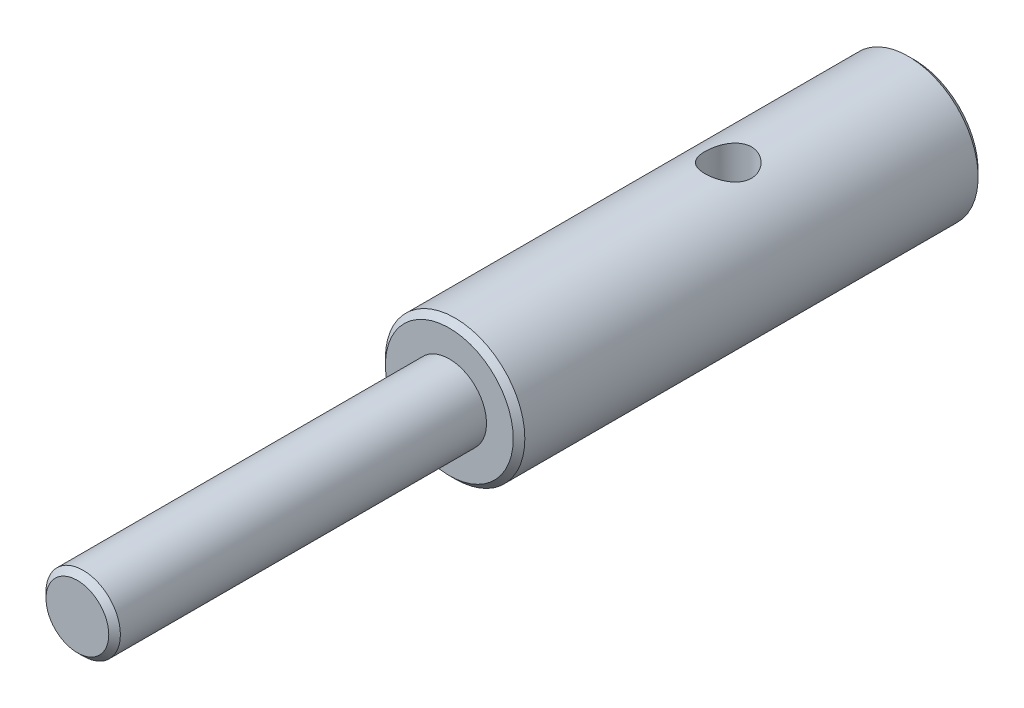
SolidWorks part; units mm, degrees
material "Unlegierter Baustahl"
ref_plane "Ebene vorne" through (0, 0, 0) normal (0, 0, 1) x (1, 0, 0)
ref_plane "Ebene oben" through (0, 0, 0) normal (0, 1, 0) x (1, 0, 0)
ref_plane "Ebene rechts" through (0, 0, 0) normal (1, 0, 0) x (0, 0, -1)
sketch "Skizze1" plane through (0, 0, 0) normal (1, 0, 0) x (0, 0, -1)
  line L0 (0, 0) -> (-32.0536, 0) construction
  line L1 (0, 1) -> (10, 1)
  line L2 (10, 1) -> (10, 3)
  line L3 (10, 3) -> (-10, 3)
  line L4 (0, 1) -> (0, 0)
  line L5 (0, 0) -> (-26, 0)
  line L6 (-26, 0) -> (-26, 1.6)
  line L7 (0, 3) -> (0, 0) construction
  line L8 (-26, 1.6) -> (-10, 1.6)
  line L9 (-10, 1.6) -> (-10, 3)
  dimension "D1" = 2
  dimension "D2" = 10
  dimension "D3" = 6
  dimension "D4" = 20
  dimension "D5" = 16
  dimension "D6" = 3.2
revolve "Rotation1" add sketch "Skizze1" angle 360 about L0
sketch "Skizze2" plane through (0, 0, 0) normal (0, 1, 0) x (1, 0, 0)
  line L0 (0, 10) -> (0, 2) construction
  line L1 (3, 10) -> (-3, 10) construction
  circle A0 centre (0, 2) radius 1
  dimension "D1" = 2
  dimension "D2" = 8
extrude "Schnitt-Linear austragen1" cut sketch "Skizze2" along normal through all
chamfer "Fase1" distance 0.25 angle 45 3 edges at (-1.6, 0, 26) (-3, 0, -10) (-3, 0, 10)
